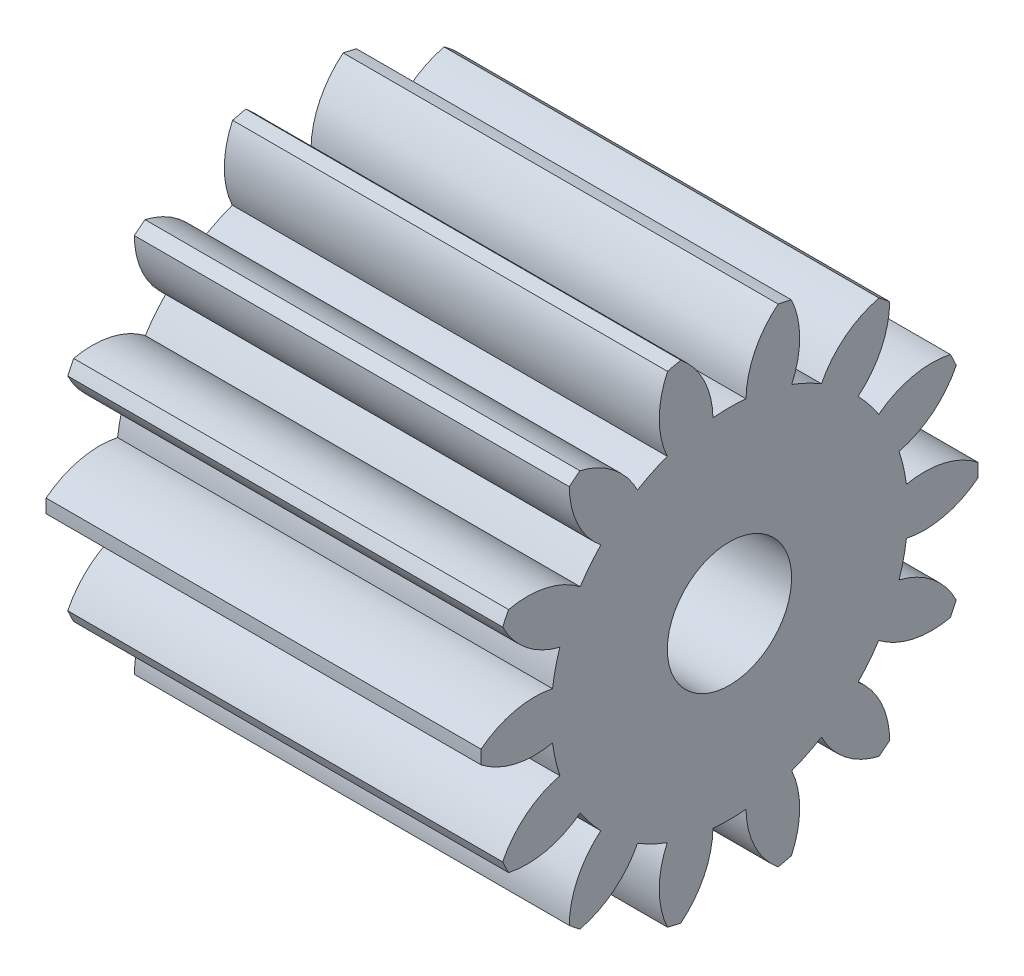
SolidWorks part; units mm, degrees
ref_plane "Plane1" through (0, 0, 0) normal (0, 0, 1) x (1, 0, 0)
ref_plane "Plane2" through (0, 0, 0) normal (0, 1, 0) x (1, 0, 0)
ref_plane "Plane3" through (0, 0, 0) normal (1, 0, 0) x (0, 0, -1)
sketch "HoldingSke" plane through (0, 0, 0) normal (0, 1, 0) x (1, 0, 0)
  line L0 (0, 0) -> (3.8812, -0.9677)
  line L1 (-15, 0) -> (100, 0) construction
  line L2 (0, 0) -> (-2.1039, 2.3779)
  line L3 (0, 0) -> (-11.863, 4.5341)
  line L4 (0, 0) -> (8.3795, 2.0892)
  line L5 (0, 0) -> (-46.8476, -17.4728)
  line L6 (0, 0) -> (-2.9014, -1.9576)
  line L7 (-2.1039, 2.3779) -> (8.6586, 51.2059)
  line L8 (-76.2, 54.61) -> (-76.1, 54.61)
  line L9 (-71.009, 38.7566) -> (-53.1078, 45.2721)
  line L10 (-76.2, 71.12) -> (104.1128, 71.12)
  line L11 (0, 0) -> (-3.5, 0)
  line L12 (-76.2, 101.6) -> (-76.192, 101.6)
  line L13 (24.9733, 27.94) -> (52.9518, 28.4284)
  line L14 (24.9733, 27.94) -> (24.9743, 27.94)
  line L15 (24.9733, 27.94) -> (100.4006, 29.5858)
  line L16 (-63.627, -0.25) -> (-12.827, -0.25)
  circle A0 centre (0, 0) radius 0.5
  circle A1 centre (0, 0) radius 1.4365
  circle A2 centre (0, 0) radius 37.5
  circle A3 centre (0, 0) radius 0.5
  dimension "MHD" = 2.873
  dimension "Hub_dia" = 75
  dimension "Bore" = 1
  dimension "MBD" = 1
  dimension "Num_teeth" = 14
  dimension "Pitch" = 4
  dimension "Overall_len" = 50
  dimension "Show_teeth" = 14
  dimension "Thickness" = 3.5
  dimension "OAL" = 50.0001
  dimension "T_dim" = 0.1
  dimension "Ap" = 20
  dimension "H" = 19.05
  dimension "Pitch_radius" = 180.3128
  dimension "Width" = 3.5
  dimension "Backlash" = 0.008
  dimension "Addendum_fac" = 1
  dimension "Dedendum_fac" = 1.25
  dimension "Clearance_fac" = 0.25
  dimension "Dedendum_add" = 0.001
  dimension "Module" = 0.25
sketch "BasProSke" plane through (0, 0, 0) normal (0, 1, 0) x (1, 0, 0)
  line L0 (-10, 0) -> (60, 0) construction
  line L1 (0, 0) -> (0, 2)
  line L2 (0, 0) -> (3.5, 0)
  line L3 (3.5, 0) -> (3.5, 2)
  line L4 (3.5, 2) -> (0, 2)
  dimension "Thickness" = 3.5
  dimension "Diameter" = 4
revolve "Base-Revolve" add sketch "BasProSke" angle 360 about L0
sketch "TooCutSke" plane through (0, 0, 0) normal (1, 0, 0) x (0, 0, -1)
  line L1 (0, 0) -> (0, 107) construction
  line L2 (0, 0) -> (-0.2099, 1.7374) construction
  line L3 (0, 0) -> (-0.7746, 3.3938) construction
  line L4 (-0.2099, 1.7374) -> (-0.3873, 1.6969) construction
  arc A0 (0.1329, 1.4303) -> (-0.1329, 1.4303) centre (0, 0) ccw
  arc A1 (0.418, 1.9818) -> (-0.418, 1.9818) centre (0, 0) ccw
  circle A2 centre (0, 0) radius 1.75 construction
  circle A3 centre (0, 0) radius 1.6445 construction
  arc A4 (-0.1329, 1.4303) -> (-0.418, 1.9818) centre (-0.8328, 1.418) ccw
  arc A5 (0.418, 1.9818) -> (0.1329, 1.4303) centre (0.8328, 1.418) ccw
  dimension "Root_dia" = 2.873
  dimension "Overcut_dia" = 4.0508
  dimension "Pitch_dia" = 3.5
  dimension "Base_dia" = 3.2889
  dimension "Flank_rad" = 0.7
  dimension "Half_ang" = 12.857
  dimension "Half_CT" = 0.1819
extrude "ToothCut" cut sketch "TooCutSke" along normal through all
fillet "Breaks" [suppressed] radius 0.005
fillet "RootFillets" [suppressed] radius 0.0635
pattern_circular "TeethCuts" count 14 every 25.714 about axis through (-10, 0, 0) along (1, 0, 0) of "ToothCut", "RootFillets", "Breaks"
sketch "HubNeaOneSke" plane through (0, 0, 0) normal (-1, 0, 0) x (0, 0, 1)
  circle A0 centre (0, 0) radius 1.4365
  dimension "Diameter" = 2.873
extrude "HubNearOne" [suppressed] add sketch "HubNeaOneSke" along normal blind 46.5001
sketch "HubNeaBotSke" plane through (0, 0, 0) normal (-1, 0, 0) x (0, 0, 1)
  circle A0 centre (0, 0) radius 1.4365
  dimension "Diameter" = 2.873
extrude "HubNearBoth" [suppressed] add sketch "HubNeaBotSke" along normal blind 23.25
ref_plane "FarPln" through (3.5, 0, 0) normal (1, 0, 0) x (0, 0, -1)
sketch "HubFarSke" plane through (3.5, 0, 0) normal (1, 0, 0) x (0, 0, -1)
  circle A0 centre (0, 0) radius 1.4365
  dimension "Diameter" = 2.873
extrude "HubFar" [suppressed] add sketch "HubFarSke" along normal blind 23.25
sketch "BorSke" plane through (0, 0, 0) normal (1, 0, 0) x (0, 0, -1)
  circle A0 centre (0, 0) radius 0.5
  dimension "Diameter" = 1
extrude "Bore" cut sketch "BorSke" along normal mid plane 100.0001
sketch "KeySke" plane through (0, 0, 0) normal (1, 0, 0) x (0, 0, -1)
  line L0 (-0.05, 0) -> (-0.05, 0.6)
  line L1 (-0.05, 0.6) -> (0.05, 0.6)
  line L2 (0.05, 0.6) -> (0.05, 0)
  line L3 (0, 0) -> (0, 34) construction
  line L4 (-0.05, 0) -> (0.05, 0)
  dimension "Offset" = 0.6
  dimension "Width" = 0.1
extrude "Keyway" [suppressed] cut sketch "KeySke" along normal mid plane 100.0001
pattern_circular "Keyway2" [suppressed] count 2 every 90 about axis through (-10, 0, 0) along (1, 0, 0)
equation "' \"Module@HoldingSke\" = 6.35"
equation "' \"Num_teeth@HoldingSke\" = 12"
equation "' \"Ap@HoldingSke\" =  20"
equation "' \"Ap@HoldingSke\" = 20"
equation "' \"Width@HoldingSke\" = 0.5 * 25.4"
equation "' \"Hub_dia@HoldingSke\"= 1 * 25.4"
equation "' \"Hub_dia@HoldingSke\" = 1 * 25.4"
equation "' \"Overall_len@HoldingSke\" = 1.0 * 25.4"
equation "' \"Bore@HoldingSke\" = 0.75 * 25.4"
equation "' \"T_dim@HoldingSke\" = 0.1 * 25.4"
equation "' \"Width@KeySke\" = 0.25 * 25.4"
equation "' \"Show_teeth@HoldingSke\" = 13"
equation "' \"Backlash@HoldingSke\" = 0.009 * 25.4"
equation "' \"Addendum_fac@HoldingSke\" = 1.0"
equation "' \"Dedendum_fac@HoldingSke\" = 1.25"
equation "' \"Dedendum_add@HoldingSke\" = 0.00005 * 25.4"
equation "' \"Clearance_fac@HoldingSke\" = 0.25"
equation "\"Pitch@HoldingSke\" = 1 / \"Module@HoldingSke\""
equation "\"Overcut_dia@TooCutSke\" = (\"Num_teeth@HoldingSke\" + 2 * \"Addendum_fac@HoldingSke\") / \"Pitch@HoldingSke\" + 0.002 * 25.4"
equation "\"Pitch_dia@TooCutSke\" = \"Num_teeth@HoldingSke\" / \"Pitch@HoldingSke\""
equation "\"Base_dia@TooCutSke\" = \"Num_teeth@HoldingSke\" / \"Pitch@HoldingSke\" * cos((\"Ap@HoldingSke\"  * 3.14159265 / 180))"
equation "\"Root_dia@TooCutSke\" = (\"Num_teeth@HoldingSke\" + 2) / \"Pitch@HoldingSke\" - 2 * (\"Addendum_fac@HoldingSke\" + \"Dedendum_fac@HoldingSke\") / \"Pitch@HoldingSke\" - \"Dedendum_add@HoldingSke\" * 2"
equation "\"Half_ang@TooCutSke\" = 180 / \"Num_teeth@HoldingSke\""
equation "\"Half_CT@TooCutSke\" = \"Num_teeth@HoldingSke\" / \"Pitch@HoldingSke\" * sin((3.14159265 / 2 / \"Num_teeth@HoldingSke\")) / 2 - 7 * \"Backlash@HoldingSke\" / 4"
equation "\"Flank_rad@TooCutSke\" = \"Num_teeth@HoldingSke\" / \"Pitch@HoldingSke\" / 5"
equation "\"Radius@RootFillets\" = \"Clearance_fac@HoldingSke\" / \"Pitch@HoldingSke\" + \"Dedendum_add@HoldingSke\""
equation "\"Break_rad@Breaks\" = 0.02 / \"Pitch@HoldingSke\""
equation "\"Thickness@HoldingSke\" = \"Width@HoldingSke\""
equation "\"OAL@HoldingSke\" = \"Thickness@HoldingSke\""
equation "\"MHD@HoldingSke\" = (\"Num_teeth@HoldingSke\" + 2) / \"Pitch@HoldingSke\" - 2 * (\"Addendum_fac@HoldingSke\" + \"Dedendum_fac@HoldingSke\")  / \"Pitch@HoldingSke\" - \"Dedendum_add@HoldingSke\" * 2"
equation "\"MBD@HoldingSke\" = (\"Num_teeth@HoldingSke\" + 2) / \"Pitch@HoldingSke\" - 2 * (\"Addendum_fac@HoldingSke\" + \"Dedendum_fac@HoldingSke\")  / \"Pitch@HoldingSke\" - \"Dedendum_add@HoldingSke\" * 2 - 0.002 * 25.4"
equation "\"MHD@HoldingSke\" = ((sgn( \"MHD@HoldingSke\" - \"Hub_dia@HoldingSke\" )-1)*( \"MHD@HoldingSke\" - \"Hub_dia@HoldingSke\" ))/-2+ \"Hub_dia@HoldingSke\""
equation "\"MBD@HoldingSke\" = ((sgn( \"MBD@HoldingSke\" - \"Bore@HoldingSke\" )-1)*( \"MBD@HoldingSke\" - \"Bore@HoldingSke\" ))/-2+ \"Bore@HoldingSke\""
equation "\"OAL@HoldingSke\" = ((sgn( \"OAL@HoldingSke\" - \"Overall_len@HoldingSke\" )+1)*( \"OAL@HoldingSke\" - \"Overall_len@HoldingSke\" ))/2 + \"Overall_len@HoldingSke\" + 0.000002 * 25.4"
equation "\"Num_teeth@TeethCuts\" = int( \"Show_teeth@HoldingSke\" ) + 1"
equation "\"Num_teeth@TeethCuts\" = ((sgn( \"Num_teeth@TeethCuts\" - \"Num_teeth@HoldingSke\" )-1)*( \"Num_teeth@TeethCuts\" - \"Num_teeth@HoldingSke\" ))/-2+ \"Num_teeth@HoldingSke\""
equation "\"Num_teeth@TeethCuts\" = ((sgn( \"Num_teeth@TeethCuts\" - 2.0)+1)*( \"Num_teeth@TeethCuts\" - 2.0))/2 +2.0"
equation "\"Angle@TeethCuts\" = 360.0 / \"Num_teeth@HoldingSke\""
equation "\"Diameter@BasProSke\" = (\"Num_teeth@HoldingSke\" + 2 * \"Addendum_fac@HoldingSke\") / \"Pitch@HoldingSke\""
equation "\"Thickness@BasProSke\"  = \"Thickness@HoldingSke\""
equation "' \"Fillet_rad@BasProSke\" =  \"Thickness@HoldingSke\" * 0.05"
equation "' \"Fillet_rad@BasProSke\" = \"Thickness@HoldingSke\" * 0.05"
equation "\"MHD@HoldingSke\" = ((sgn( \"MHD@HoldingSke\" - \"Root_dia@TooCutSke\" )-1)*( \"MHD@HoldingSke\" - \"Root_dia@TooCutSke\" ))/-2+ \"Root_dia@TooCutSke\""
equation "\"Diameter@HubNeaOneSke\" = \"MHD@HoldingSke\""
equation "\"Length@HubNearOne\" = \"OAL@HoldingSke\" - \"Thickness@BasProSke\""
equation "\"Diameter@HubNeaBotSke\" = \"MHD@HoldingSke\""
equation "\"Length@HubNearBoth\" = ( \"OAL@HoldingSke\" - \"Thickness@BasProSke\" ) / 2.0"
equation "\"Thickness@FarPln\" = \"Thickness@BasProSke\""
equation "\"Diameter@HubFarSke\" = \"MHD@HoldingSke\""
equation "\"Length@HubFar\" = ( \"OAL@HoldingSke\" - \"Thickness@BasProSke\" ) / 2.0"
equation "\"Diameter@BorSke\" = \"MBD@HoldingSke\""
equation "\"D1@Bore\" = \"OAL@HoldingSke\" * 2.0"
equation "\"D1@Keyway\" = \"OAL@HoldingSke\" * 2.0"
equation "\"Offset@KeySke\" = \"T_dim@HoldingSke\" + \"MBD@HoldingSke\" / 2.0"
